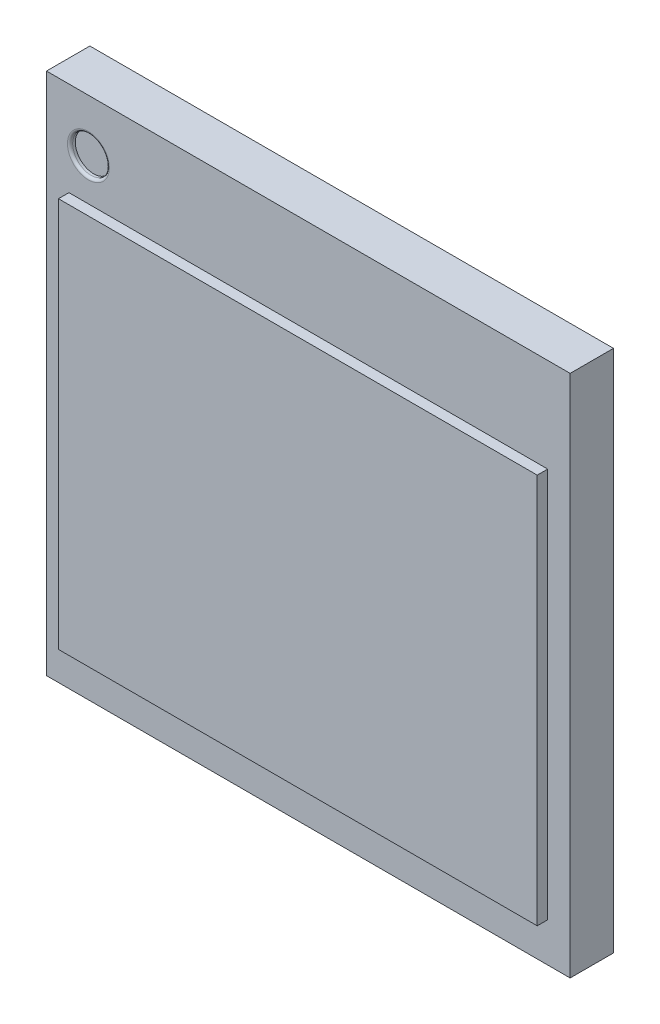
SolidWorks part; units mm, degrees
ref_plane "Front Plane" through (0, 0, 0) normal (0, 0, 1) x (1, 0, 0)
ref_plane "Top Plane" through (0, 0, 0) normal (0, 1, 0) x (1, 0, 0)
ref_plane "Right Plane" through (0, 0, 0) normal (1, 0, 0) x (0, 0, -1)
sketch "Sketch1" plane through (0, 0, 0) normal (0, 0, 1) x (1, 0, 0)
  line L0 (2.5, 2.5) -> (-2.5, -2.5) construction
  line L1 (-2.5, 2.5) -> (2.5, 2.5)
  line L2 (-2.5, 2.5) -> (-2.5, -2.5)
  line L3 (-2.5, -2.5) -> (2.5, -2.5)
  line L4 (2.5, 2.5) -> (2.5, -2.5)
  line L5 (-2.5, 2.5) -> (2.5, -2.5) construction
  point P4 (0, 0)
  dimension "D2" = 5
  dimension "D4" = 5
extrude "Boss-Extrude1" add sketch "Sketch1" along normal blind 0.414 from offset 0.21
ref_plane "Plane1" through (0, 1.9, 0) normal (0, 1, 0) x (1, 0, 0)
sketch "Sketch3" plane through (0, 1.9, 0) normal (0, 1, 0) x (1, 0, 0)
  line L0 (0, 0) -> (-2.1273, 0) construction
  line L1 (-1.96, -0.1575) -> (-1.96, 0.2665) construction
  line L2 (-1.96, 0) -> (-1.96, -0.315)
  arc A0 (-1.96, 0) -> (-1.96, -0.315) centre (-1.96, -0.1575) ccw
  dimension "D2" = 0.315
  dimension "D1" = 1.96
revolve "Revolve1" add sketch "Sketch3" angle 360 about L1
pattern_linear "LPattern1" count 6 spacing 0.75 along (0, -1, 0) count 6 spacing 0.8 along (1, 0, 0) skipping (2, 1), (2, 2), (2, 3), (2, 4), (3, 1), (3, 2), (3, 3), (3, 4) of "Revolve1"
sketch "Sketch4" plane through (0, 0, 0.624) normal (0, 0, 1) x (1, 0, 0)
  line L0 (2.5, 2.5) -> (-2.5, 2.5) construction
  line L1 (-2.5, 2.5) -> (-2.5, -2.5) construction
  circle A0 centre (-2.1, 2) radius 0.175
  dimension "D3" = 0.35
  dimension "D1" = 0.5
  dimension "D2" = 0.4
extrude "Cut-Extrude1" cut sketch "Sketch4" against normal blind 0.05 contours A0
fillet "Fillet1" radius 0.025 1 edges at (-1.925, 2, 0.624)
sketch "Sketch5" plane through (0, 0, 0.624) normal (0, 0, 1) x (1, 0, 0)
  line L1 (-2.2858, 1.6014) -> (2.2858, 1.6014)
  line L2 (-2.2858, 1.6014) -> (-2.2858, -2.1257)
  line L3 (-2.2858, -2.1257) -> (2.2858, -2.1257)
  line L4 (2.2858, 1.6014) -> (2.2858, -2.1257)
  line L5 (-2.2858, 1.6014) -> (2.2858, -2.1257) construction
  line L6 (-2.2858, -2.1257) -> (2.2858, 1.6014) construction
  point P0 (0, -0.2622)
extrude "Boss-Extrude2" add sketch "Sketch5" along normal blind 0.1
